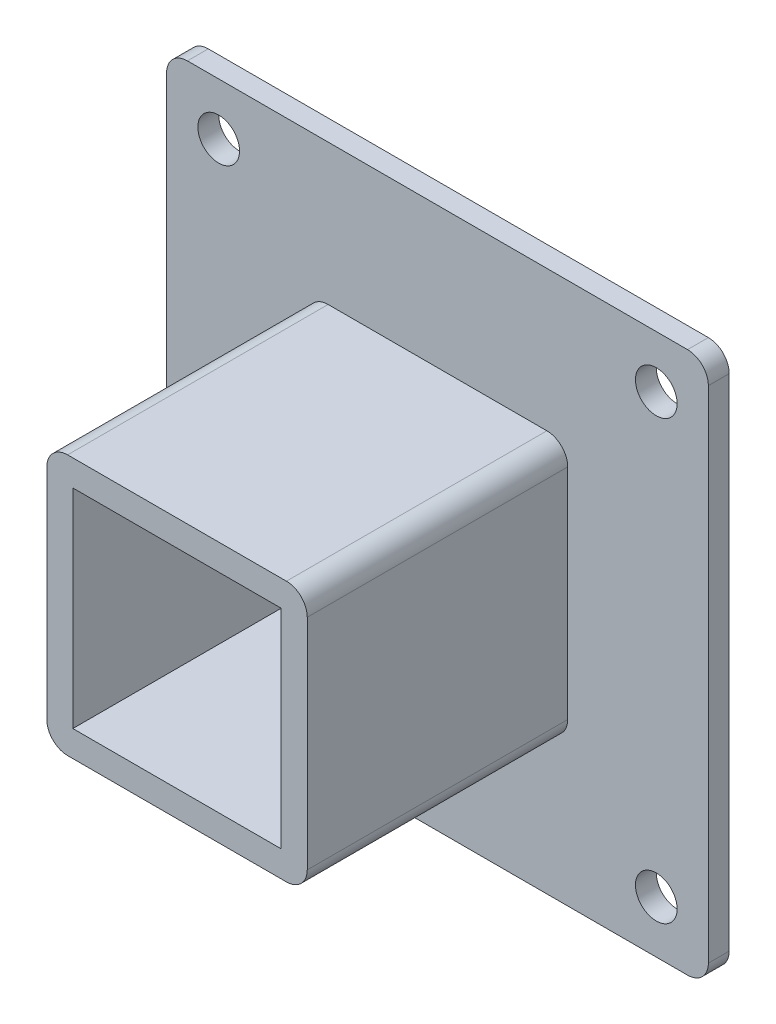
SolidWorks part; units mm, degrees
ref_plane "前视基准面" through (0, 0, 0) normal (0, 0, 1) x (1, 0, 0)
ref_plane "上视基准面" through (0, 0, 0) normal (0, 1, 0) x (1, 0, 0)
ref_plane "右视基准面" through (0, 0, 0) normal (1, 0, 0) x (0, 0, -1)
other "Configuration Table"
sketch "草图1" plane through (0, 0, 0) normal (0, 0, 1) x (1, 0, 0)
  line L1 (-12.5, 12.5) -> (12.5, 12.5)
  line L2 (-12.5, 12.5) -> (-12.5, -12.5)
  line L3 (-12.5, -12.5) -> (12.5, -12.5)
  line L4 (12.5, 12.5) -> (12.5, -12.5)
  line L5 (-12.5, 12.5) -> (12.5, -12.5) construction
  line L6 (-12.5, -12.5) -> (12.5, 12.5) construction
  line L7 (-10, 10) -> (10, 10)
  line L8 (-10, 10) -> (-10, -10)
  line L9 (-10, -10) -> (10, -10)
  line L10 (10, 10) -> (10, -10)
  line L11 (-10, 10) -> (10, -10) construction
  line L12 (-10, -10) -> (10, 10) construction
  point P0 (0, 0)
  point P6 (0, 0)
  dimension "D1" = 25
  dimension "D2" = 25
  dimension "D3" = 20
extrude "凸台-拉伸1" add sketch "草图1" along normal blind 25
sketch "草图3" plane through (0, 0, 0) normal (0, 0, -1) x (-1, 0, 0)
  line L1 (-26, 26) -> (26, 26)
  line L2 (-26, 26) -> (-26, -26)
  line L3 (-26, -26) -> (26, -26)
  line L4 (26, 26) -> (26, -26)
  line L5 (-26, 26) -> (26, -26) construction
  line L6 (-26, -26) -> (26, 26) construction
  point P0 (0, 0)
  dimension "D1" = 52
  dimension "D2" = 52
extrude "凸台-拉伸2" add sketch "草图3" along normal blind 2
sketch "草图4" plane through (0, 0, -2) normal (0, 0, -1) x (-1, 0, 0)
  line L1 (-10, 10) -> (10, 10)
  line L2 (-10, 10) -> (-10, -10)
  line L3 (-10, -10) -> (10, -10)
  line L4 (10, 10) -> (10, -10)
  line L5 (-10, 10) -> (10, -10) construction
  line L6 (-10, -10) -> (10, 10) construction
  point P0 (0, 0)
  dimension "D1" = 20
  dimension "D2" = 20
extrude "切除-拉伸1" cut sketch "草图4" against normal through all
fillet "圆角1" radius 2 1 edges at (-26, 26, -1)
fillet "圆角2" radius 2 1 edges at (-26, -26, -1)
fillet "圆角3" radius 2 1 edges at (26, -26, -1)
fillet "圆角4" radius 2 1 edges at (26, 26, -1)
fillet "圆角5" radius 2 1 edges at (-12.5, -12.5, 12.5)
fillet "圆角6" radius 2 1 edges at (-12.5, 12.5, 12.5)
fillet "圆角7" radius 2 1 edges at (12.5, 12.5, 12.5)
fillet "圆角8" radius 2 1 edges at (12.5, -12.5, 12.5)
sketch "草图5" plane through (0, 0, -2) normal (0, 0, -1) x (-1, 0, 0)
  line L0 (-25.4142, 25.4142) -> (25.4142, -25.4142) construction
  line L1 (25.4142, 25.4142) -> (-25.4142, -25.4142) construction
  line L2 (24, 26) -> (-24, 26) construction
  line L3 (-24, -26) -> (24, -26) construction
  arc A0 (-24, 26) -> (-26, 24) centre (-24, 24) ccw construction
  arc A1 (24, -26) -> (26, -24) centre (24, -24) ccw construction
  arc A2 (26, 24) -> (24, 26) centre (24, 24) ccw construction
  arc A3 (-26, -24) -> (-24, -26) centre (-24, -24) ccw construction
  circle A4 centre (-21, 21) radius 2
  circle A5 centre (21, 21) radius 2
  circle A6 centre (-21, -21) radius 2
  circle A7 centre (21, -21) radius 2
  dimension "D1" = 4
  dimension "D2" = 4
  dimension "D3" = 4
  dimension "D4" = 4
  dimension "D5" = 5
  dimension "D6" = 5
  dimension "D7" = 5
  dimension "D8" = 5
extrude "切除-拉伸2" cut sketch "草图5" against normal through all
